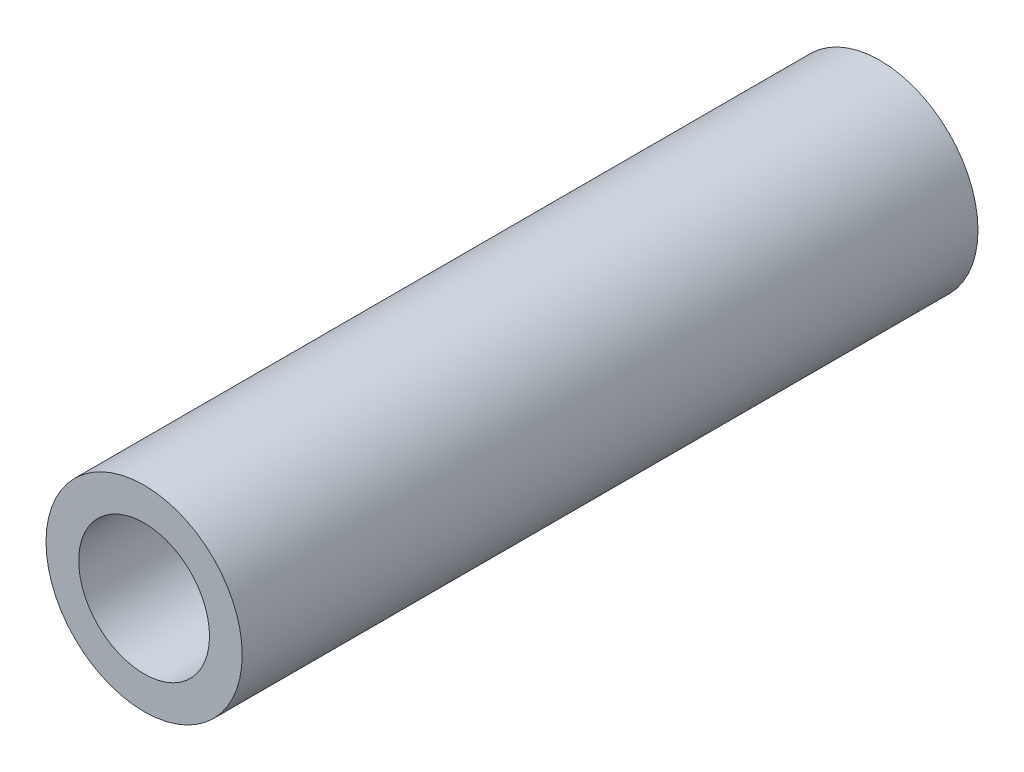
SolidWorks part; units mm, degrees
material "PVC Rigid"
ref_plane "Front Plane" through (0, 0, 0) normal (0, 0, 1) x (1, 0, 0)
ref_plane "Top Plane" through (0, 0, 0) normal (0, 1, 0) x (1, 0, 0)
ref_plane "Right Plane" through (0, 0, 0) normal (1, 0, 0) x (0, 0, -1)
sketch "Sketch1" plane through (0, 0, 0) normal (0, 0, 1) x (1, 0, 0)
  circle A0 centre (0, 0) radius 7.62
  circle A2 centre (0, 0) radius 5.08
  dimension "D1" = 15.24
  dimension "D2" = 10.16
extrude "Boss-Extrude1" add sketch "Sketch1" along normal blind 57.15
